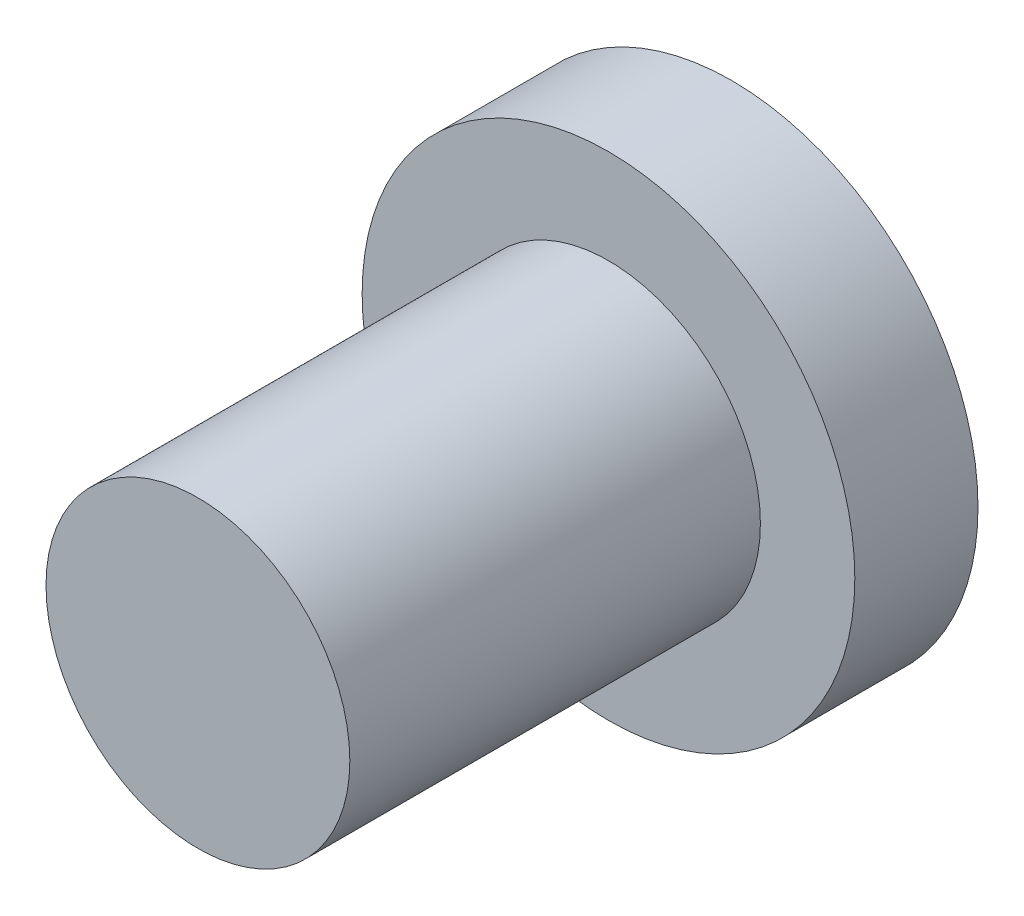
SolidWorks part; units mm, degrees
ref_plane "Plano frontal" through (0, 0, 0) normal (0, 0, 1) x (1, 0, 0)
ref_plane "Plano superior" through (0, 0, 0) normal (0, 1, 0) x (1, 0, 0)
ref_plane "Plano direito" through (0, 0, 0) normal (1, 0, 0) x (0, 0, -1)
sketch "Sketch1" plane through (0, 0, 0) normal (0, 0, 1) x (1, 0, 0)
  circle A0 centre (0, 0) radius 6
  dimension "D1" = 12
extrude "Boss-Extrude1" add sketch "Sketch1" along normal mid plane 3
sketch "Sketch2" plane through (0, 0, 1.5) normal (0, 0, 1) x (1, 0, 0)
  circle A0 centre (0, 0) radius 3.7
  dimension "D1" = 7.4
extrude "Boss-Extrude2" add sketch "Sketch2" along normal blind 10
